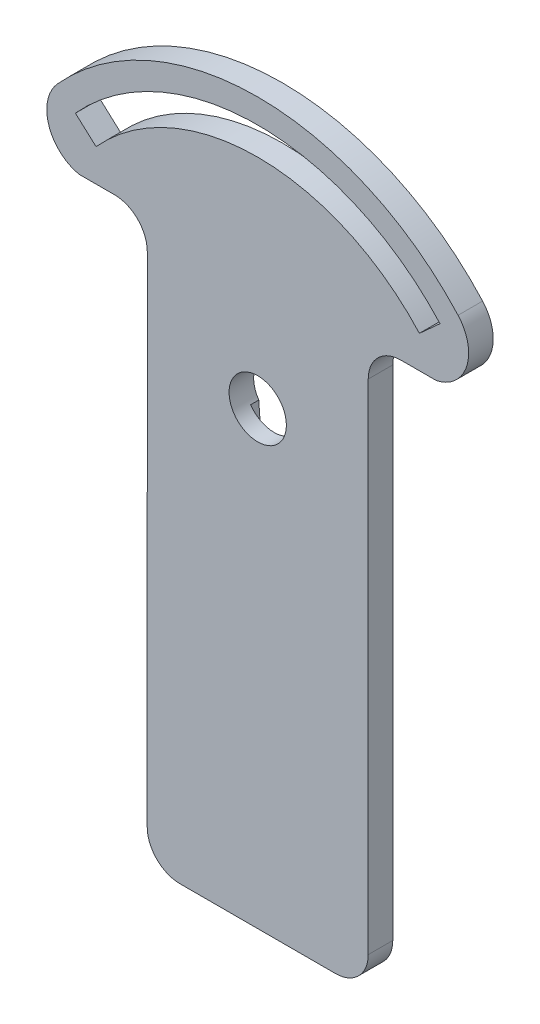
SolidWorks part; units mm, degrees
ref_plane "Alzado" through (0, 0, 0) normal (0, 0, 1) x (1, 0, 0)
ref_plane "Planta" through (0, 0, 0) normal (0, 1, 0) x (1, 0, 0)
ref_plane "Vista lateral" through (0, 0, 0) normal (1, 0, 0) x (0, 0, -1)
sketch "Corte exterior" plane through (0, 0, 0) normal (0, 0, 1) x (1, 0, 0)
  line L0 (39.5043, -30.6861) -> (20.5043, -30.6861)
  line L1 (12.511, 38.2118) -> (8.1613, 38.2118)
  line L2 (16.5043, -26.6861) -> (16.511, 34.2118)
  line L3 (43.5043, 34.2118) -> (43.5043, -26.6861)
  line L4 (16.5043, -26.6861) -> (16.511, 34.2118)
  line L5 (10.2531, 42.1758) -> (7.7314, 44.4563)
  line L6 (52.2773, 44.4563) -> (49.7555, 42.1758)
  line L7 (47.5043, 38.2118) -> (51.8473, 38.2118)
  arc A0 (16.511, 34.2118) -> (12.511, 38.2118) centre (12.511, 34.2118) ccw
  arc A1 (47.5043, 38.2118) -> (43.5043, 34.2118) centre (47.5043, 34.2118) ccw
  arc A2 (39.5043, -30.6861) -> (43.5043, -26.6861) centre (39.5043, -26.6861) ccw
  arc A3 (16.5043, -26.6861) -> (20.5043, -30.6861) centre (20.5043, -26.6861) ccw
  arc A4 (49.7555, 42.1758) -> (10.2531, 42.1758) centre (30.0043, 24.3139) ccw
  arc A5 (52.2773, 44.4563) -> (7.7314, 44.4563) centre (30.0043, 24.3139) ccw
  circle A6 centre (30.0043, 24.3139) radius 3.5
  arc A7 (54.4801, 46.4484) -> (5.5286, 46.4484) centre (30.0043, 24.3139) ccw
  arc A8 (5.5286, 46.4484) -> (8.1613, 38.2118) centre (9.237, 43.0947) ccw
  arc A9 (51.8473, 38.2118) -> (54.4801, 46.4484) centre (50.7716, 43.0947) ccw
sketch "Grabado Superficie" plane through (0, 0, 0) normal (0, 0, 1) x (1, 0, 0)
  line L0 (32.8737, 22.3097) -> (31.9994, 9.9231)
  line L1 (28.0093, 9.9231) -> (27.135, 22.3097)
  arc A0 (28.0093, 9.9231) -> (31.9994, 9.9231) centre (30.0043, 10.0639) ccw
  arc A1 (27.135, 22.3097) -> (32.8737, 22.3097) centre (30.0043, 24.3139) ccw
sketch "grabado linea medio" plane through (0, 0, 0) normal (0, 0, 1) x (1, 0, 0)
  line L0 (43.48, -26.0526) -> (35.34, -26.0487)
  line L1 (35.34, -26.0487) -> (35.3377, -30.6887)
  line L2 (32.8178, -30.6875) -> (32.82, -26.0462)
  line L3 (32.82, -26.0462) -> (16.4801, -25.8383)
  line L4 (16.4912, -2.8096) -> (32.8312, -2.8175)
  line L5 (32.8312, -2.8175) -> (32.8335, 1.8225)
  line L6 (32.8335, 1.8225) -> (35.3535, 1.8213)
  line L7 (35.3535, 1.8213) -> (35.3512, -2.8187)
  line L8 (35.3512, -2.8187) -> (39.4112, -2.8206)
  line L9 (39.4112, -2.8206) -> (39.4073, -10.9006)
  line L10 (39.4073, -10.9006) -> (43.4873, -10.9026)
  line L11 (16.4912, -2.8096) -> (16.4801, -25.8383)
  line L12 (32.8178, -30.6875) -> (35.3377, -30.6887)
  line L13 (43.48, -26.0526) -> (43.4873, -10.9026)
extrude "Saliente-Extruir1" add sketch "Corte exterior" along normal blind 3 contours L7 A9 A7 A8 L1 A0 L2 A3 L0 A2 L3 A1 A5 L6 A4 L5 A6
extrude "Cortar-Extruir1" cut sketch "Grabado Superficie" along normal blind 1
extrude "Cortar-Extruir2" cut sketch "grabado linea medio" along normal blind 0.1
